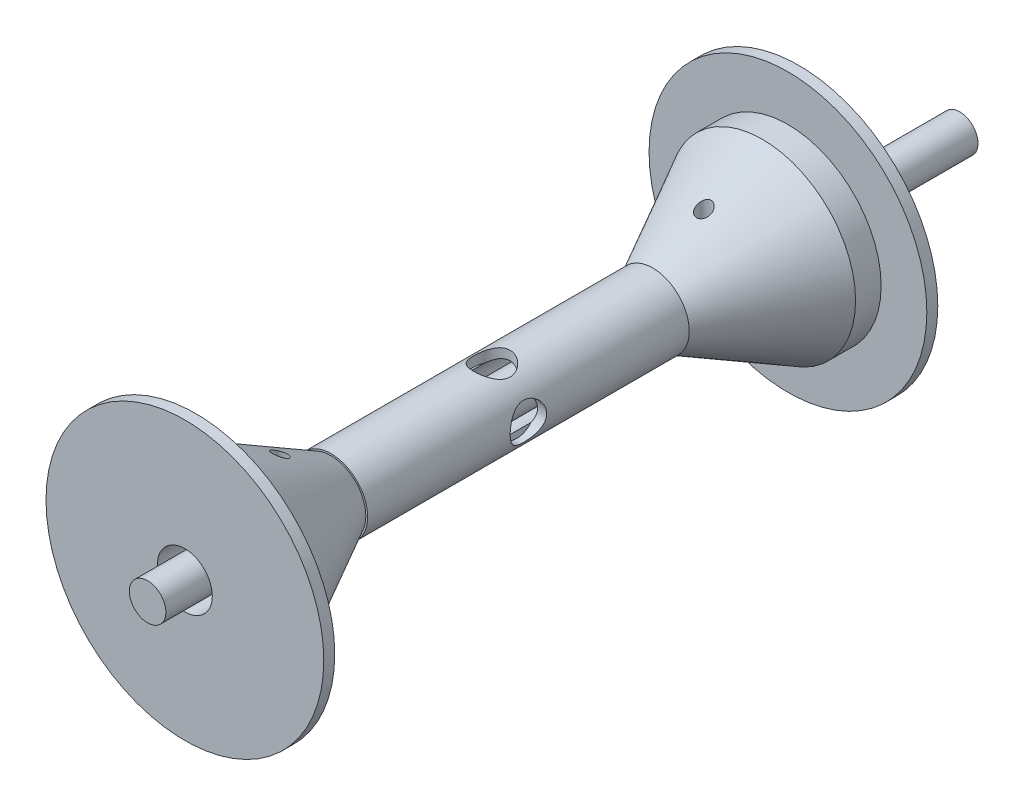
SolidWorks part; units mm, degrees
ref_plane "Front Plane" through (0, 0, 0) normal (0, 0, 1) x (1, 0, 0)
ref_plane "Top Plane" through (0, 0, 0) normal (0, 1, 0) x (1, 0, 0)
ref_plane "Right Plane" through (0, 0, 0) normal (1, 0, 0) x (0, 0, -1)
sketch "Sketch1" plane through (0, 0, 0) normal (0, 0, 1) x (1, 0, 0)
  circle A0 centre (0, 0) radius 6.35
  dimension "D1" = 12.7
extrude "Boss-Extrude1" add sketch "Sketch1" along normal blind 282.194
ref_plane "Plane1" through (0, 0, 5.08) normal (0, 0, -1) x (-1, 0, 0)
sketch "Sketch3" plane through (0, 0, 5.08) normal (0, 0, -1) x (-1, 0, 0)
  circle A0 centre (0, 0) radius 30.48
  dimension "D1" = 60.96
ref_plane "Plane2" through (0, 0, 55.88) normal (0, 0, -1) x (-1, 0, 0)
sketch "Sketch4" plane through (0, 0, 55.88) normal (0, 0, -1) x (-1, 0, 0)
  circle A0 centre (0, 0) radius 9.525
  dimension "D1" = 19.05
ref_plane "Plane3" through (0, 0, 141.097) normal (0, 0, 1) x (1, 0, 0)
ref_axis "Axis1" through (0, 0, 282.194) along (0, 0, -1)
sketch "Sketch8" plane through (0, 0, 55.88) normal (0, 0, -1) x (-1, 0, 0)
  circle A0 centre (0, 0) radius 12.7
  dimension "D1" = 25.4
sketch "Sketch11" plane through (0, 0, 55.88) normal (0, 0, -1) x (-1, 0, 0)
  circle A0 centre (0, 0) radius 30.48
  dimension "D1" = 60.96
ref_plane "Plane4" through (0, 0, 106.68) normal (0, 0, -1) x (-1, 0, 0)
sketch "Sketch12" plane through (0, 0, 106.68) normal (0, 0, -1) x (-1, 0, 0)
  circle A0 centre (0, 0) radius 9.525
  dimension "D1" = 19.05
sketch "Sketch14" plane through (0, 0, 0) normal (1, 0, 0) x (0, 0, -1)
  line L0 (-106.68, -6.985) -> (-106.68, 6.985) construction
  line L1 (-55.88, -30.48) -> (-55.88, 30.48) construction
  line L2 (-106.68, 9.525) -> (-55.88, 9.525)
  line L3 (-106.68, -9.525) -> (-106.68, 9.525) construction
  line L4 (-55.88, -9.525) -> (-55.88, 9.525) construction
  line L5 (-55.88, 9.525) -> (-55.88, 32.385)
  line L6 (-106.68, 12.065) -> (-106.68, 9.525)
  line L7 (-106.68, 9.525) -> (-55.88, 9.525) construction
  line L8 (-282.194, 0) -> (0, 0) construction
  line L10 (-55.88, 32.385) -> (-68.58, 32.385)
  line L11 (-68.58, 32.385) -> (-106.68, 12.065)
  dimension "D1" = 12.7
  dimension "D2" = 22.86
  dimension "D3" = 9.525
  dimension "D4" = 2.54
revolve "Revolve1" add sketch "Sketch14" angle 360 about axis through (0, 0, 282.194) along (0, 0, -1)
ref_plane "Plane5" through (0, 0, 162.56) normal (0, 0, -1) x (-1, 0, 0)
sketch "Sketch15" plane through (0, 0, 0) normal (1, 0, 0) x (0, 0, -1)
  line L0 (-55.88, -30.48) -> (-55.88, 30.48) construction
  line L1 (-55.88, 22.86) -> (-59.69, 22.86)
  line L2 (-55.88, 22.86) -> (-55.88, 48.26)
  line L3 (-55.88, 48.26) -> (-59.69, 48.26)
  line L4 (-59.69, 22.86) -> (-59.69, 48.26)
  line L5 (-282.194, 0) -> (0, 0) construction
  dimension "D1" = 25.4
  dimension "D2" = 3.81
  dimension "D3" = 22.86
revolve "Revolve2" add sketch "Sketch15" angle 360 about axis through (0, 0, 282.194) along (0, 0, -1)
combine bodies "Combine1" operation type add bodies to combine 127 126
mirror "Mirror4" about plane through (0, 0, 162.56) normal (0, 0, -1) of bodies 147
sketch "Sketch18" plane through (0, 0, 0) normal (0, 1, 0) x (1, 0, 0)
  line L0 (0, -106.68) -> (-12.7, -106.68) construction
  line L1 (9.525, -106.68) -> (-9.525, -106.68) construction
  line L2 (-12.7, -106.68) -> (-9.525, -106.68)
  line L3 (-12.7, -106.68) -> (-12.7, -218.44)
  line L4 (12.065, -218.44) -> (-12.065, -218.44) construction
  line L5 (-12.7, -218.44) -> (-9.525, -218.44)
  line L6 (9.525, -218.44) -> (-9.525, -218.44) construction
  line L7 (-9.525, -218.44) -> (-9.525, -106.68)
  dimension "D1" = 12.7
  dimension "D2" = 3.175
revolve "Revolve4" add sketch "Sketch18" angle 360 about axis through (0, 0, 282.194) along (0, 0, -1)
sketch "Sketch16" plane through (0, 0, 0) normal (0, 1, 0) x (1, 0, 0)
  line L0 (0, -282.194) -> (0, 0) construction
  line L1 (53.086, -162.56) -> (-53.086, -162.56) construction
  circle A0 centre (0, -88.9) radius 2.54
  circle A2 centre (0, -236.22) radius 2.54
  dimension "D1" = 5.08
  dimension "D3" = 5.08
  dimension "D4" = 73.66
  dimension "D5" = 73.66
extrude "Cut-Extrude1" cut sketch "Sketch16" against normal through all both and the other way through all
sketch "Sketch19" plane through (0, 0, 0) normal (0, 1, 0) x (1, 0, 0)
  line L0 (53.086, -162.56) -> (-53.086, -162.56) construction
  line L1 (0, -282.194) -> (0, 0) construction
  circle A0 centre (0, -162.56) radius 6.35
  dimension "D1" = 12.7
extrude "Cut-Extrude2" cut sketch "Sketch19" against normal blind 17.78 from offset 25.4
sketch "Sketch20" plane through (0, 0, 0) normal (1, 0, 0) x (0, 0, -1)
  line L0 (-162.56, -53.086) -> (-162.56, 53.086) construction
  line L1 (-282.194, 0) -> (0, 0) construction
  circle A0 centre (-162.56, 0) radius 6.35
  dimension "D1" = 12.7
extrude "Cut-Extrude3" cut sketch "Sketch20" against normal blind 16.764 from offset 25.4
equation "\"A\"=0.5"
equation "\"D1@Sketch1\"=\"A\""
equation "\"B\"=0.2"
equation "\"D1@Sketch16\"=\"B\""
